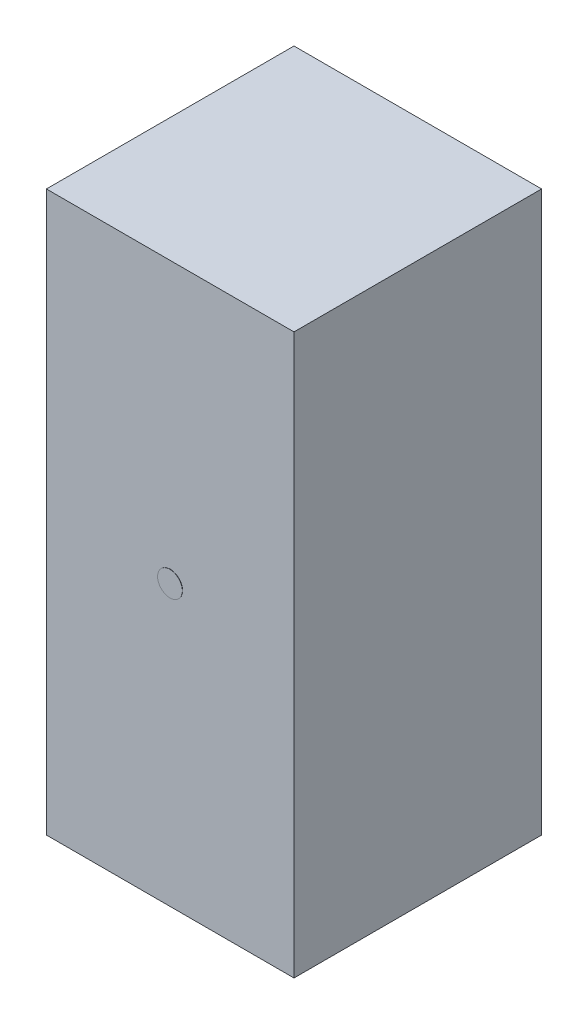
SolidWorks part; units mm, degrees
ref_plane "Alzado" through (0, 0, 0) normal (0, 0, 1) x (1, 0, 0)
ref_plane "Planta" through (0, 0, 0) normal (0, 1, 0) x (1, 0, 0)
ref_plane "Vista lateral" through (0, 0, 0) normal (1, 0, 0) x (0, 0, -1)
sketch "Sketch1" plane through (0, 0, 0) normal (0, 1, 0) x (1, 0, 0)
  line L1 (-50, 50) -> (50, 50)
  line L2 (-50, 50) -> (-50, -50)
  line L3 (-50, -50) -> (50, -50)
  line L4 (50, 50) -> (50, -50)
  line L5 (-50, 50) -> (50, -50) construction
  line L6 (-50, -50) -> (50, 50) construction
  point P0 (0, 0)
  dimension "D1" = 100
  dimension "D2" = 100
extrude "Boss-Extrude1" add sketch "Sketch1" along normal blind 226
sketch "Sketch2" plane through (0, 0, 50) normal (0, 0, 1) x (1, 0, 0)
  line L0 (-50, 226) -> (-50, 0) construction
  circle A0 centre (0, 113) radius 5
  point P4 (-50, 113)
  dimension "D1" = 10
extrude "Boss-Extrude2" add sketch "Sketch2" along normal blind 0.1
